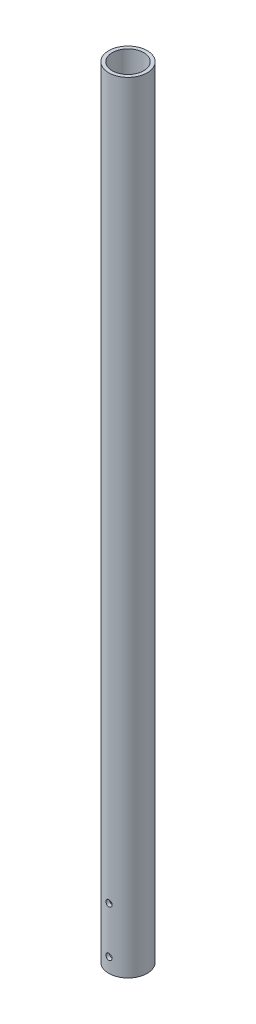
SolidWorks part; units mm, degrees
ref_plane "Front Plane" through (0, 0, 0) normal (0, 0, 1) x (1, 0, 0)
ref_plane "Top Plane" through (0, 0, 0) normal (0, 1, 0) x (1, 0, 0)
ref_plane "Right Plane" through (0, 0, 0) normal (1, 0, 0) x (0, 0, -1)
sketch "Sketch1" plane through (0, 0, 0) normal (0, 1, 0) x (1, 0, 0)
  circle A0 centre (0, 0) radius 21.082
  circle A1 centre (0, 0) radius 17.272
  dimension "D1" = 34.544
  dimension "1.66" = 42.164
extrude "Boss-Extrude1" add sketch "Sketch1" along normal blind 855.6625
ref_plane "Plane1" through (0, 0, 21.082) normal (0, 0, 1) x (1, 0, 0)
sketch "Sketch2" plane through (0, 0, 21.082) normal (0, 0, 1) x (1, 0, 0)
  line L2 (-21.082, 0) -> (21.082, 0) construction
  point P0 (0, 15.875)
  point P1 (0, 66.675)
  dimension "D2" = 15.875
  dimension "D3" = 50.8
hole_wizard "1/4 Clearance Hole1" positions "Sketch3" profile "Sketch4" hole size "1/4" standard "ANSI Inch" end condition through all
sketch "Sketch3" plane through (0, 0, 21.082) normal (0, 0, 1) x (1, 0, 0)
  point P0 (0, 15.875)
  point P3 (0, 66.675)
sketch "Sketch4" plane through (0, 15.875, 21.082) normal (1, 0, 0) x (0, -1, 0)
  line L0 (0, 0) -> (0, 42.164)
  line L1 (0, 42.164) -> (3.3782, 42.164)
  line L2 (3.3782, 42.164) -> (3.3782, 0)
  line L5 (3.3782, 0) -> (0, 0)
  line L11 (0, -6.35) -> (0, 107.95) construction
  dimension "Thru Hole Dia." = 6.7564
  dimension "Thru Hole Depth" = 42.164
